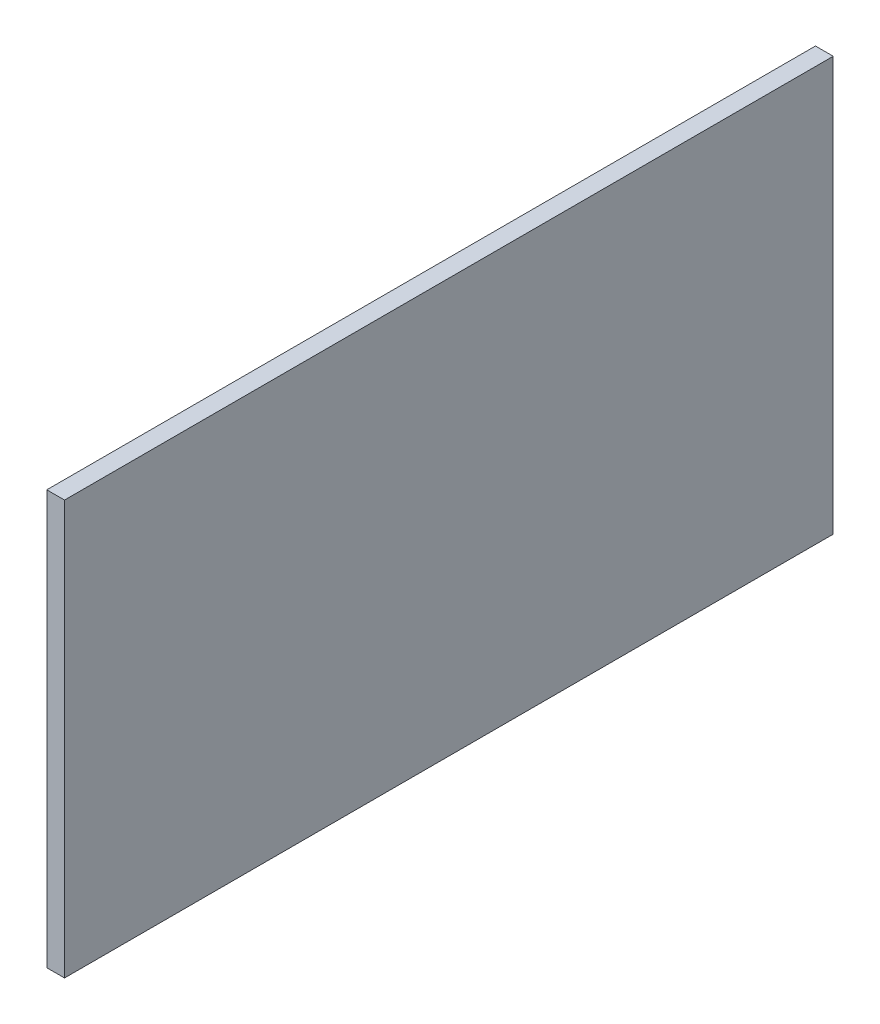
SolidWorks part; units mm, degrees
ref_plane "Front Plane" through (0, 0, 0) normal (0, 0, 1) x (1, 0, 0)
ref_plane "Top Plane" through (0, 0, 0) normal (0, 1, 0) x (1, 0, 0)
ref_plane "Right Plane" through (0, 0, 0) normal (1, 0, 0) x (0, 0, -1)
sketch "Sketch1" plane through (0, 0, 0) normal (1, 0, 0) x (0, 0, -1)
  line L1 (-71.2403, 0) -> (58.7597, 0)
  line L2 (-71.2403, 0) -> (-71.2403, 70)
  line L3 (-71.2403, 70) -> (58.7597, 70)
  line L4 (58.7597, 0) -> (58.7597, 70)
  dimension "D1" = 70
  dimension "D2" = 130
extrude "Boss-Extrude1" add sketch "Sketch1" along normal blind 3
